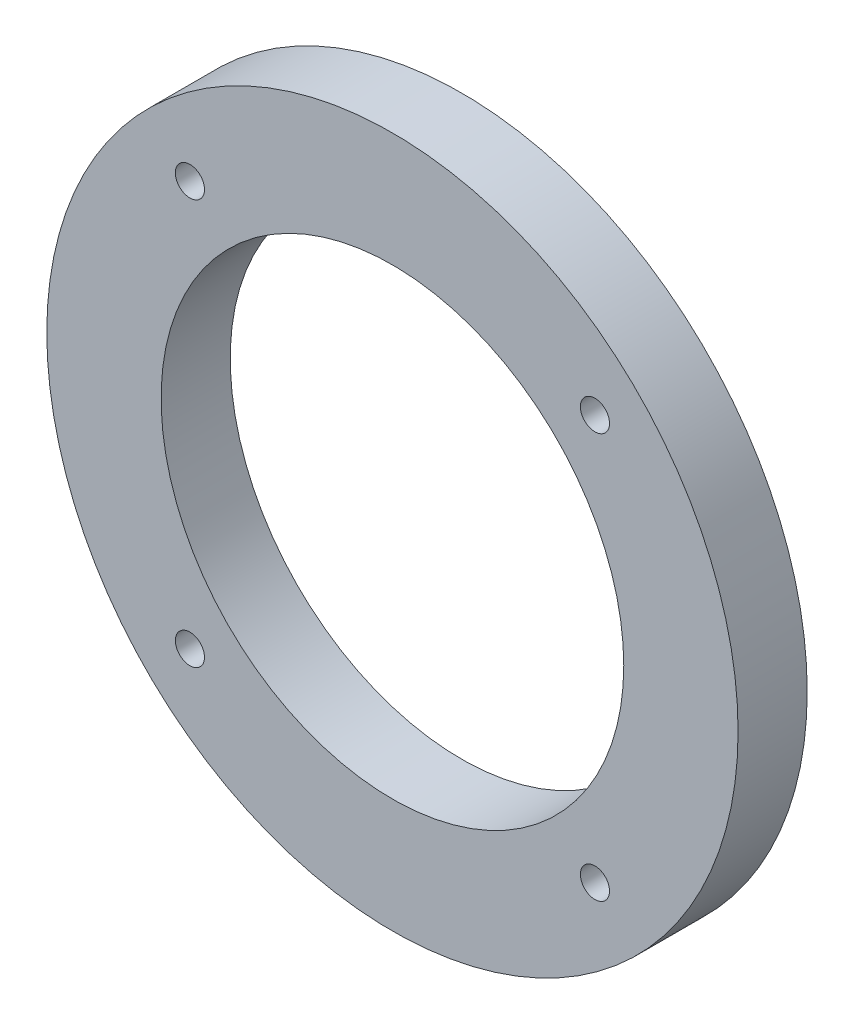
SolidWorks part; units mm, degrees
ref_plane "Front Plane" through (0, 0, 0) normal (0, 0, 1) x (1, 0, 0)
ref_plane "Top Plane" through (0, 0, 0) normal (0, 1, 0) x (1, 0, 0)
ref_plane "Right Plane" through (0, 0, 0) normal (1, 0, 0) x (0, 0, -1)
sketch "Sketch1" plane through (0, 0, 0) normal (0, 0, 1) x (1, 0, 0)
  line L0 (0, 0) -> (0, 35) construction
  line L1 (0, 0) -> (-35, 0) construction
  line L2 (0, 0) -> (-24.7487, 24.7487) construction
  circle A0 centre (0, 0) radius 35
  circle A1 centre (0, 0) radius 23.425
  circle A2 centre (-20.5061, 20.5061) radius 1.475
  circle A4 centre (20.5061, 20.5061) radius 1.475
  circle A5 centre (20.5061, -20.5061) radius 1.475
  circle A6 centre (-20.5061, -20.5061) radius 1.475
  point P18 (0, 0)
  dimension "D1" = 70
  dimension "D2" = 46.85
  dimension "D3" = 2.95
  dimension "D5" = 45
  dimension "D4" = 29
  dimension "D6" = 4
extrude "Boss-Extrude1" add sketch "Sketch1" along normal blind 7
